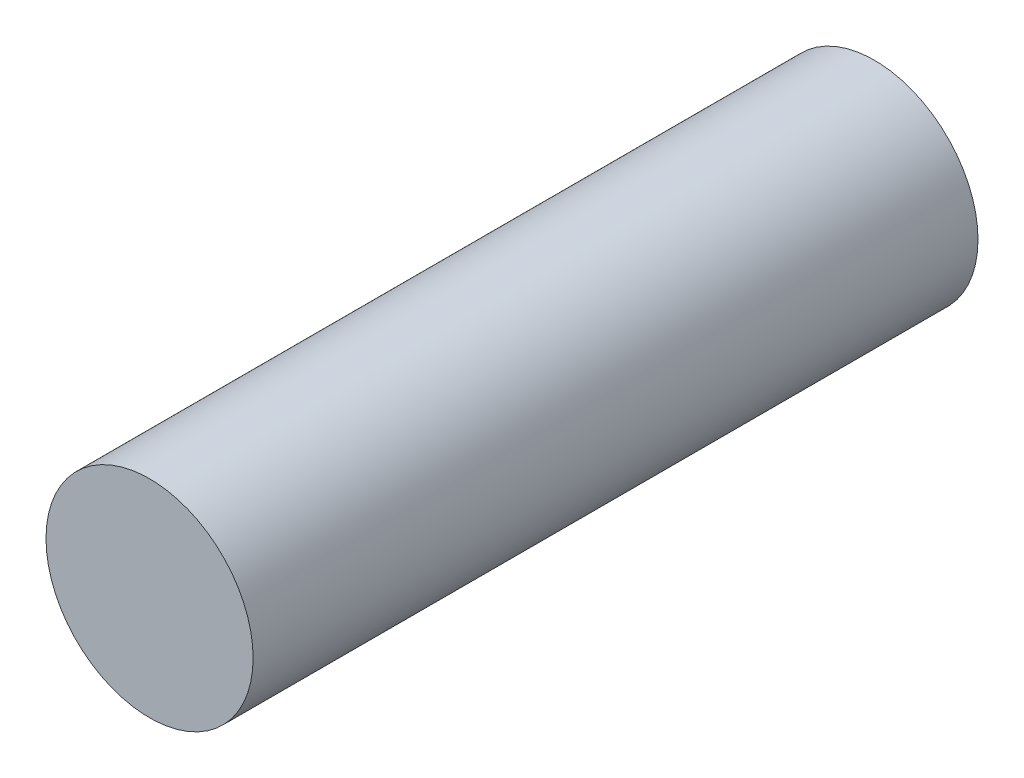
SolidWorks part; units mm, degrees
ref_plane "Front Plane" through (0, 0, 0) normal (0, 0, 1) x (1, 0, 0)
ref_plane "Top Plane" through (0, 0, 0) normal (0, 1, 0) x (1, 0, 0)
ref_plane "Right Plane" through (0, 0, 0) normal (1, 0, 0) x (0, 0, -1)
sketch "Sketch1" plane through (0, 0, 0) normal (0, 0, 1) x (1, 0, 0)
  circle A0 centre (0, 0.2318) radius 0.635
  dimension "D1" = 1.27
extrude "Boss-Extrude1" add sketch "Sketch1" along normal blind 4.445
